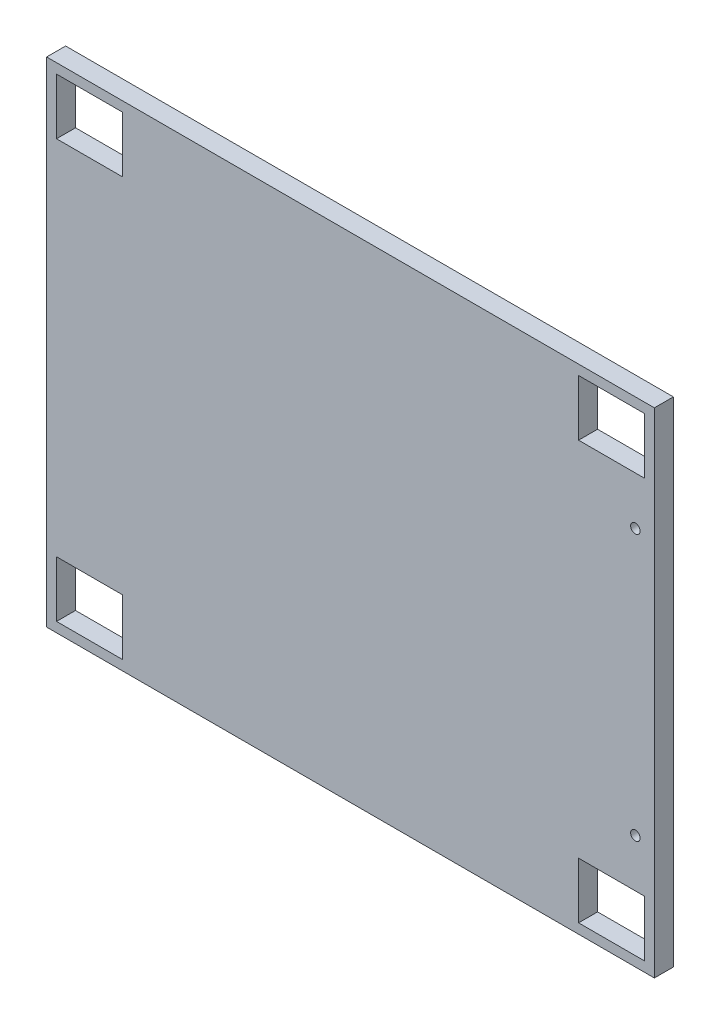
SolidWorks part; units mm, degrees
ref_plane "Front Plane" through (0, 0, 0) normal (0, 0, 1) x (1, 0, 0)
ref_plane "Top Plane" through (0, 0, 0) normal (0, 1, 0) x (1, 0, 0)
ref_plane "Right Plane" through (0, 0, 0) normal (1, 0, 0) x (0, 0, -1)
sketch "Sketch1" plane through (0, 0, 0) normal (0, 0, 1) x (1, 0, 0)
  line L0 (47.1117, 72.0896) -> (47.1117, 53.3571)
  line L1 (-130.7518, 75.3916) -> (72.4482, 75.3916)
  line L2 (-130.7518, 75.3916) -> (-130.7518, -89.7084)
  line L3 (-130.7518, -89.7084) -> (72.4482, -89.7084)
  line L4 (72.4482, 75.3916) -> (72.4482, -89.7084)
  line L5 (-29.1518, 75.3916) -> (-29.1518, -89.7084) construction
  line L6 (-107.8918, 46.8099) -> (49.5882, 46.8099) construction
  line L7 (-127.4498, 72.0896) -> (-105.4153, 72.0896)
  line L8 (-127.4498, 72.0896) -> (-127.4498, 53.3571)
  line L9 (-127.4498, 53.3571) -> (-105.4153, 53.3571)
  line L10 (-105.4153, 72.0896) -> (-105.4153, 53.3571)
  line L11 (-127.4498, 72.0896) -> (-105.4153, 53.3571) construction
  line L12 (-127.4498, 53.3571) -> (-105.4153, 72.0896) construction
  line L13 (47.1117, 72.0896) -> (69.1462, 72.0896)
  line L14 (69.1462, 72.0896) -> (69.1462, 53.3571)
  line L15 (47.1117, 53.3571) -> (69.1462, 53.3571)
  line L16 (47.1117, 53.3571) -> (69.1462, 72.0896) construction
  line L17 (47.1117, 72.0896) -> (69.1462, 53.3571) construction
  line L18 (47.1117, -67.6739) -> (47.1117, -86.4064)
  line L19 (47.1117, -67.6739) -> (69.1462, -67.6739)
  line L20 (69.1462, -67.6739) -> (69.1462, -86.4064)
  line L21 (47.1117, -86.4064) -> (69.1462, -86.4064)
  line L22 (47.1117, -86.4064) -> (69.1462, -67.6739) construction
  line L23 (47.1117, -67.6739) -> (69.1462, -86.4064) construction
  line L24 (-127.4498, -67.6739) -> (-127.4498, -86.4064)
  line L25 (-127.4498, -67.6739) -> (-105.4153, -67.6739)
  line L26 (-105.4153, -67.6739) -> (-105.4153, -86.4064)
  line L27 (-127.4498, -86.4064) -> (-105.4153, -86.4064)
  line L28 (-127.4498, -86.4064) -> (-105.4153, -67.6739) construction
  line L29 (-127.4498, -67.6739) -> (-105.4153, -86.4064) construction
  line L30 (-107.8918, 46.8099) -> (-107.8918, -9.0701) construction
  line L31 (-107.8918, -9.0701) -> (49.5882, -9.0701) construction
  line L32 (49.5882, 46.8099) -> (49.5882, -9.0701) construction
  line L33 (-79.9518, -16.6588) -> (21.6482, -16.6588) construction
  line L34 (-79.9518, -16.6588) -> (-79.9518, -69.9988) construction
  line L35 (-79.9518, -69.9988) -> (21.6482, -69.9988) construction
  line L36 (21.6482, -16.6588) -> (21.6482, -69.9988) construction
  circle A0 centre (66.0982, 37.2916) radius 1.5875
  circle A1 centre (66.0982, -51.6084) radius 1.5875
  point P0 (0, 0)
  point P6 (-116.4325, 62.7234)
  point P12 (58.129, 62.7234)
  point P18 (58.129, -77.0401)
  point P23 (-116.4325, -77.0401)
  point P36 (-29.1518, 46.8099)
  point P37 (-29.1518, -16.6588)
  dimension "D12" = 3.175
  dimension "D13" = 6.35
  dimension "D1" = 203.2
  dimension "D2" = 165.1
  dimension "D3" = 18.7325
  dimension "D4" = 22.0345
  dimension "D5" = 3.302
  dimension "D8" = 157.48
  dimension "D9" = 55.88
  dimension "D10" = 101.6
  dimension "D11" = 53.34
  dimension "D15" = 38.1
  dimension "D16" = 3.302
  dimension "D17" = 3.302
  dimension "D18" = 3.302
  dimension "D6" = 2
  dimension "D7" = 2
  dimension "D14" = 2
extrude "Boss-Extrude1" add sketch "Sketch1" along normal blind 6.35
